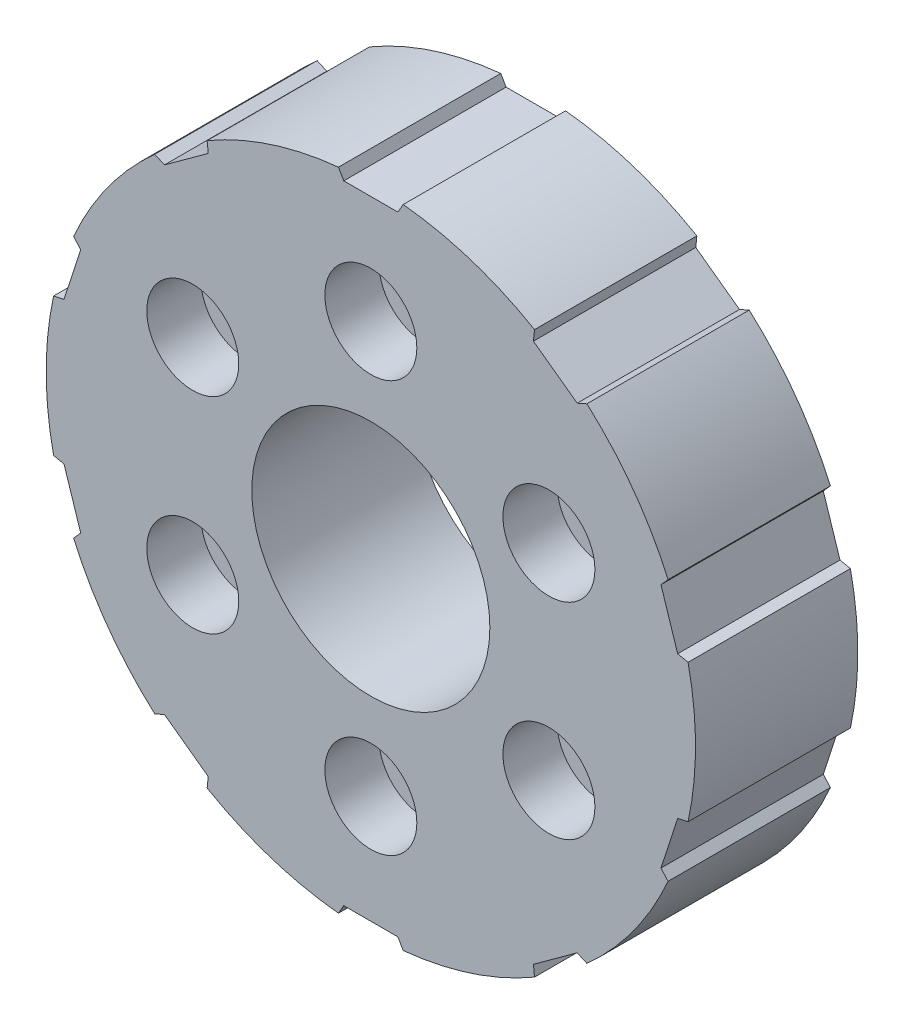
SolidWorks part; units mm, degrees
material "201 Annealed Stainless Steel (SS)"
ref_plane "Front" through (0, 0, 0) normal (0, 0, 1) x (1, 0, 0)
ref_plane "Top" through (0, 0, 0) normal (0, 1, 0) x (1, 0, 0)
ref_plane "Right" through (0, 0, 0) normal (1, 0, 0) x (0, 0, -1)
sketch "Sketch1" plane through (0, 0, 0) normal (0, 0, 1) x (1, 0, 0)
  line L0 (0, 38.7123) -> (0, 0) construction
  line L1 (-2.5, 29) -> (2.5, 29)
  line L2 (2.5, 29) -> (2.991, 29.8505)
  line L3 (-2.5, 29) -> (-2.991, 29.8505)
  line L4 (19.0683, 21.992) -> (19.9655, 22.3915)
  line L5 (15.0232, 24.931) -> (19.0683, 21.992)
  line L6 (15.0232, 24.931) -> (15.1259, 25.9077)
  line L7 (28.3532, 6.5839) -> (29.3138, 6.3797)
  line L8 (26.8081, 11.3391) -> (28.3532, 6.5839)
  line L9 (26.8081, 11.3391) -> (27.4652, 12.069)
  line L10 (26.8081, -11.3391) -> (27.4652, -12.069)
  line L11 (28.3532, -6.5839) -> (26.8081, -11.3391)
  line L12 (28.3532, -6.5839) -> (29.3138, -6.3797)
  line L13 (15.0232, -24.931) -> (15.1259, -25.9077)
  line L14 (19.0683, -21.992) -> (15.0232, -24.931)
  line L15 (19.0683, -21.992) -> (19.9655, -22.3915)
  line L16 (-2.5, -29) -> (-2.991, -29.8505)
  line L17 (2.5, -29) -> (-2.5, -29)
  line L18 (2.5, -29) -> (2.991, -29.8505)
  line L19 (-19.0683, -21.992) -> (-19.9655, -22.3915)
  line L20 (-15.0232, -24.931) -> (-19.0683, -21.992)
  line L21 (-15.0232, -24.931) -> (-15.1259, -25.9077)
  line L22 (-28.3532, -6.5839) -> (-29.3138, -6.3797)
  line L23 (-26.8081, -11.3391) -> (-28.3532, -6.5839)
  line L24 (-26.8081, -11.3391) -> (-27.4652, -12.069)
  line L25 (-26.8081, 11.3391) -> (-27.4652, 12.069)
  line L26 (-28.3532, 6.5839) -> (-26.8081, 11.3391)
  line L27 (-28.3532, 6.5839) -> (-29.3138, 6.3797)
  line L28 (-15.0232, 24.931) -> (-15.1259, 25.9077)
  line L29 (-19.0683, 21.992) -> (-15.0232, 24.931)
  line L30 (-19.0683, 21.992) -> (-19.9655, 22.3915)
  arc A0 (-2.991, 29.8505) -> (-15.1259, 25.9077) centre (0, 0) ccw
  arc A1 (15.1259, 25.9077) -> (2.991, 29.8505) centre (0, 0) ccw
  arc A2 (27.4652, 12.069) -> (19.9655, 22.3915) centre (0, 0) ccw
  arc A3 (29.3138, -6.3797) -> (29.3138, 6.3797) centre (0, 0) ccw
  arc A4 (19.9655, -22.3915) -> (27.4652, -12.069) centre (0, 0) ccw
  arc A5 (2.991, -29.8505) -> (15.1259, -25.9077) centre (0, 0) ccw
  arc A6 (-15.1259, -25.9077) -> (-2.991, -29.8505) centre (0, 0) ccw
  arc A7 (-27.4652, -12.069) -> (-19.9655, -22.3915) centre (0, 0) ccw
  arc A8 (-29.3138, 6.3797) -> (-29.3138, -6.3797) centre (0, 0) ccw
  arc A9 (-19.9655, 22.3915) -> (-27.4652, 12.069) centre (0, 0) ccw
  point P8 (0, 29)
  dimension "D1" = 60
  dimension "D2" = 2.5
  dimension "D3" = 120
  dimension "D4" = 1
  dimension "D5" = 10
extrude "Boss-Extrude1" add sketch "Sketch1" along normal blind 15
hole_wizard "M24x2.0 Tapped Hole1" positions "Sketch3" profile "Sketch2" tap size "M24x2.0" standard "ISO"
sketch "Sketch3" plane through (0, 0, 15) normal (0, 0, 1) x (1, 0, 0)
  point P0 (0, 0)
sketch "Sketch2" plane through (0, 0, 15) normal (1, 0, 0) x (0, -1, 0)
  line L0 (0, 0) -> (0, 64.6095)
  line L1 (0, 64.6095) -> (11, 58)
  line L2 (11, 58) -> (11, 0)
  line L5 (11, 0) -> (0, 0)
  line L10 (0, 64.6095) -> (-11, 58) construction
  line L11 (0, -6.35) -> (0, 107.95) construction
  dimension "Tap Drill Dia." = 22
  dimension "Tap Drill Depth" = 58
  dimension "Drill Angle" = 118
cosmetic thread "Hole Thread1" parameters "D1"=15, "D2"=24
hole_wizard "CBORE for M5 Hex Socket Head Cap Screw1" positions "Sketch5" profile "Sketch4" counterbore size "M5" standard "ISO" end condition through all
sketch "Sketch5" plane through (0, 0, 15) normal (0, 0, 1) x (1, 0, 0)
  line L0 (0, 0) -> (0, 19) construction
  point P0 (0, 19)
  dimension "D1" = 19
sketch "Sketch4" plane through (0, 19, 15) normal (1, 0, 0) x (0, -1, 0)
  line L0 (0, 0) -> (0, 15)
  line L1 (0, 15) -> (2.75, 15)
  line L3 (2.75, 15) -> (2.75, 5)
  line L4 (2.75, 5) -> (4.25, 5)
  line L5 (4.25, 5) -> (4.25, 0)
  line L7 (4.25, 0) -> (0, 0)
  line L11 (0, -6.35) -> (0, 107.95) construction
  dimension "Thru Hole Dia." = 5.5
  dimension "Thru Hole Depth" = 15
  dimension "C'Bore Dia." = 8.5
  dimension "C'Bore Depth" = 5
pattern_circular "CirPattern3" count 6 every 60 about axis through (0, 0, 0) along (0, 0, 1) of "CBORE for M5 Hex Socket Head Cap Screw1"
